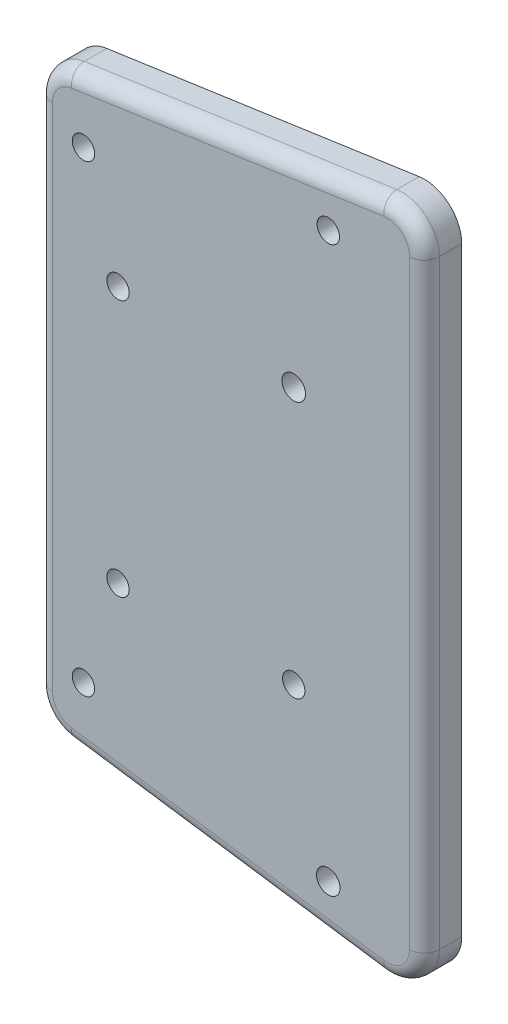
SolidWorks part; units mm, degrees
material "Plastique personnalisé"
ref_plane "Plan de face" through (0, 0, 0) normal (0, 0, 1) x (1, 0, 0)
ref_plane "Plan de dessus" through (0, 0, 0) normal (0, 1, 0) x (1, 0, 0)
ref_plane "Plan de droite" through (0, 0, 0) normal (1, 0, 0) x (0, 0, -1)
sketch "Esquisse1" plane through (0, 0, 0) normal (0, 0, 1) x (1, 0, 0)
  line L0 (20.2366, -45.19) -> (-21.6678, -39.13)
  line L1 (-25.9522, -34.1815) -> (-25.9522, 34.1815)
  line L2 (25.9522, -40.2415) -> (25.9522, 40.2415)
  line L3 (25.9522, 0) -> (-25.9522, 0) construction
  line L4 (20.2366, 45.19) -> (-21.6678, 39.13)
  arc A0 (20.2366, 45.19) -> (25.9522, 40.2415) centre (20.9522, 40.2415) cw
  arc A1 (-21.6678, 39.13) -> (-25.9522, 34.1815) centre (-20.9522, 34.1815) ccw
  arc A2 (-21.6678, -39.13) -> (-25.9522, -34.1815) centre (-20.9522, -34.1815) cw
  arc A3 (20.2366, -45.19) -> (25.9522, -40.2415) centre (20.9522, -40.2415) ccw
  circle A4 centre (13.0544, -37.7671) radius 1.5788
  circle A5 centre (-19.7867, -31.0799) radius 1.5
  circle A6 centre (8.4178, -17.2314) radius 1.5
  circle A7 centre (-15.1502, -17.2314) radius 1.5
  circle A8 centre (8.4178, 17.3136) radius 1.5821
  circle A9 centre (-15.1502, 17.2314) radius 1.5
  circle A10 centre (-19.7867, 31.0799) radius 1.5
  circle A11 centre (13.0544, 37.8459) radius 1.5
extrude "Boss.-Extru.1" add sketch "Esquisse1" along normal blind 5
fillet "Congé1" radius 2 8 edges at (-0.7156, 42.16, 5) (24.225, 44.0216, 5) (25.9522, 0, 5) (24.225, -44.0216, 5) (-0.7156, -42.16, 5) (-24.7323, -37.4542, 5) (-25.9522, 0, 5) (-24.7323, 37.4542, 5)
